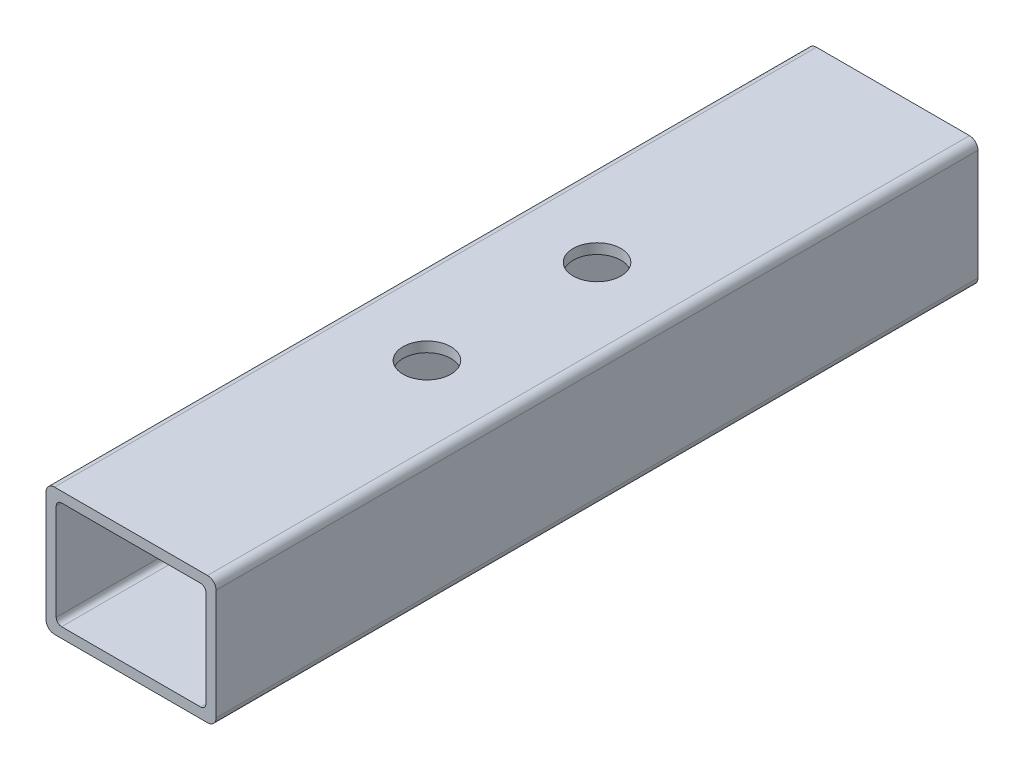
SolidWorks part; units mm, degrees
material "Plain Carbon Steel"
ref_plane "Front" through (0, 0, 0) normal (0, 0, 1) x (1, 0, 0)
ref_plane "Top" through (0, 0, 0) normal (0, 1, 0) x (1, 0, 0)
ref_plane "Right" through (0, 0, 0) normal (1, 0, 0) x (0, 0, -1)
sketch "Sketch1" plane through (0, 0, 0) normal (0, 0, 1) x (1, 0, 0)
  line L0 (-22.352, 0) -> (-25.4, 0) construction
  line L1 (22.86, -19.05) -> (-22.86, -19.05)
  line L2 (25.4, -16.51) -> (25.4, 16.51)
  line L3 (22.86, 19.05) -> (-22.86, 19.05)
  line L4 (-25.4, -16.51) -> (-25.4, 16.51)
  line L5 (25.4, -19.05) -> (-25.4, 19.05) construction
  line L6 (25.4, 19.05) -> (-25.4, -19.05) construction
  line L7 (20.7518, 16.002) -> (-20.7518, 16.002)
  line L8 (22.352, 14.4018) -> (22.352, -14.4018)
  line L9 (20.7518, -16.002) -> (-20.7518, -16.002)
  line L10 (-22.352, 14.4018) -> (-22.352, -14.4018)
  line L11 (22.352, 16.002) -> (-22.352, -16.002) construction
  line L12 (22.352, -16.002) -> (-22.352, 16.002) construction
  line L13 (0, -16.002) -> (0, -19.05) construction
  line L14 (22.352, -14.4018) -> (22.352, -19.05) construction
  line L16 (22.352, -19.05) -> (25.4, -19.05) construction
  arc A0 (-20.7518, -16.002) -> (-22.352, -14.4018) centre (-20.7518, -14.4018) cw
  arc A1 (22.352, -14.4018) -> (20.7518, -16.002) centre (20.7518, -14.4018) cw
  arc A2 (20.7518, 16.002) -> (22.352, 14.4018) centre (20.7518, 14.4018) cw
  arc A3 (-20.7518, 16.002) -> (-22.352, 14.4018) centre (-20.7518, 14.4018) ccw
  arc A4 (22.86, -19.05) -> (25.4, -16.51) centre (22.86, -16.51) ccw
  arc A5 (25.4, 16.51) -> (22.86, 19.05) centre (22.86, 16.51) ccw
  arc A6 (-22.86, 19.05) -> (-25.4, 16.51) centre (-22.86, 16.51) ccw
  arc A7 (-22.86, -19.05) -> (-25.4, -16.51) centre (-22.86, -16.51) cw
  point P0 (0, 0)
  point P6 (0, 0)
  dimension "D2" = 1.6002
  dimension "D3" = 2.54
sketch "Sketch2" plane through (0, 0, 0) normal (1, 0, 0) x (0, 0, -1)
  line L0 (-152.4, 0) -> (152.4, 0) construction
  dimension "Length" = 304.8
ref_plane "Plane1" through (25.4, 0, 0) normal (1, 0, 0) x (0, 0, -1)
sketch "Sketch5" plane through (25.4, 0, 0) normal (1, 0, 0) x (0, 0, -1)
  line L0 (-152.4, 19.05) -> (-152.4, -19.05) construction
  line L1 (152.4, 19.05) -> (152.4, -19.05) construction
sketch "Sketch4" plane through (0, 0, 0) normal (0, 0, 1) x (1, 0, 0)
  line L0 (25.4, -16.51) -> (25.4, 16.51) construction
  line L1 (22.86, 19.05) -> (-22.86, 19.05) construction
  line L2 (-25.4, -16.51) -> (-25.4, 16.51) construction
  line L3 (22.86, -19.05) -> (-22.86, -19.05) construction
  line L4 (22.352, 14.4018) -> (22.352, -14.4018) construction
  line L5 (20.7518, -16.002) -> (-20.7518, -16.002) construction
  line L6 (-22.352, 14.4018) -> (-22.352, -14.4018) construction
  line L7 (20.7518, 16.002) -> (-20.7518, 16.002) construction
  line L8 (25.4, -16.51) -> (25.4, 16.51)
  line L9 (22.86, 19.05) -> (-22.86, 19.05)
  line L10 (-25.4, -16.51) -> (-25.4, 16.51)
  line L11 (22.86, -19.05) -> (-22.86, -19.05)
  line L12 (22.352, 14.4018) -> (22.352, -14.4018)
  line L13 (20.7518, -16.002) -> (-20.7518, -16.002)
  line L14 (-22.352, 14.4018) -> (-22.352, -14.4018)
  line L15 (20.7518, 16.002) -> (-20.7518, 16.002)
  arc A0 (25.4, 16.51) -> (22.86, 19.05) centre (22.86, 16.51) ccw construction
  arc A1 (-22.86, 19.05) -> (-25.4, 16.51) centre (-22.86, 16.51) ccw construction
  arc A2 (-25.4, -16.51) -> (-22.86, -19.05) centre (-22.86, -16.51) ccw construction
  arc A3 (22.86, -19.05) -> (25.4, -16.51) centre (22.86, -16.51) ccw construction
  arc A4 (20.7518, -16.002) -> (22.352, -14.4018) centre (20.7518, -14.4018) ccw construction
  arc A5 (-22.352, -14.4018) -> (-20.7518, -16.002) centre (-20.7518, -14.4018) ccw construction
  arc A6 (-20.7518, 16.002) -> (-22.352, 14.4018) centre (-20.7518, 14.4018) ccw construction
  arc A7 (22.352, 14.4018) -> (20.7518, 16.002) centre (20.7518, 14.4018) ccw construction
  arc A8 (25.4, 16.51) -> (22.86, 19.05) centre (22.86, 16.51) ccw
  arc A9 (-22.86, 19.05) -> (-25.4, 16.51) centre (-22.86, 16.51) ccw
  arc A10 (-25.4, -16.51) -> (-22.86, -19.05) centre (-22.86, -16.51) ccw
  arc A11 (22.86, -19.05) -> (25.4, -16.51) centre (22.86, -16.51) ccw
  arc A12 (20.7518, -16.002) -> (22.352, -14.4018) centre (20.7518, -14.4018) ccw
  arc A13 (-22.352, -14.4018) -> (-20.7518, -16.002) centre (-20.7518, -14.4018) ccw
  arc A14 (-20.7518, 16.002) -> (-22.352, 14.4018) centre (-20.7518, 14.4018) ccw
  arc A15 (22.352, 14.4018) -> (20.7518, 16.002) centre (20.7518, 14.4018) ccw
extrude "Boss-Extrude1" add sketch "Sketch4" along normal blind 227.5637
sketch "Sketch6" plane through (0, 19.05, 0) normal (0, 1, 0) x (1, 0, 0)
  line L0 (0, -227.5637) -> (0, -183.6318) construction
  line L2 (-22.86, -183.6318) -> (22.86, -183.6318) construction
  line L3 (-22.86, 0) -> (-22.86, -227.5637) construction
  line L4 (22.86, 0) -> (22.86, -227.5637) construction
  line L5 (-22.86, -43.9318) -> (22.86, -43.9318) construction
  line L6 (22.86, -227.5637) -> (-22.86, -227.5637) construction
  line L7 (0, -183.6318) -> (0, -43.9318) construction
  line L8 (0, -43.9318) -> (0, 0) construction
  line L9 (22.86, 0) -> (-22.86, 0) construction
  dimension "D1" = 139.7
sketch "Sketch9" plane through (0, 19.05, 0) normal (0, 1, 0) x (1, 0, 0)
  line L0 (0, -227.5637) -> (0, -139.1818) construction
  line L1 (22.86, -227.5637) -> (-22.86, -227.5637) construction
  line L2 (0, -139.1818) -> (0, -88.3818) construction
  line L3 (0, -88.3818) -> (0, 0) construction
  circle A0 centre (0, -139.1818) radius 7.1437
  circle A1 centre (0, -88.3818) radius 7.1437
  dimension "D2" = 14.2875
  dimension "D1" = 50.8
extrude "Cut-Extrude2" cut sketch "Sketch9" along direction (0, -1, 0) on the side against the normal up to next (3.048 mm away)
equation "\"D3@Sketch1\"=\"Outside Width@Sketch1\"*.05"
equation "\"D2@Sketch1\"=\"D1@Sketch1\"*.05"
